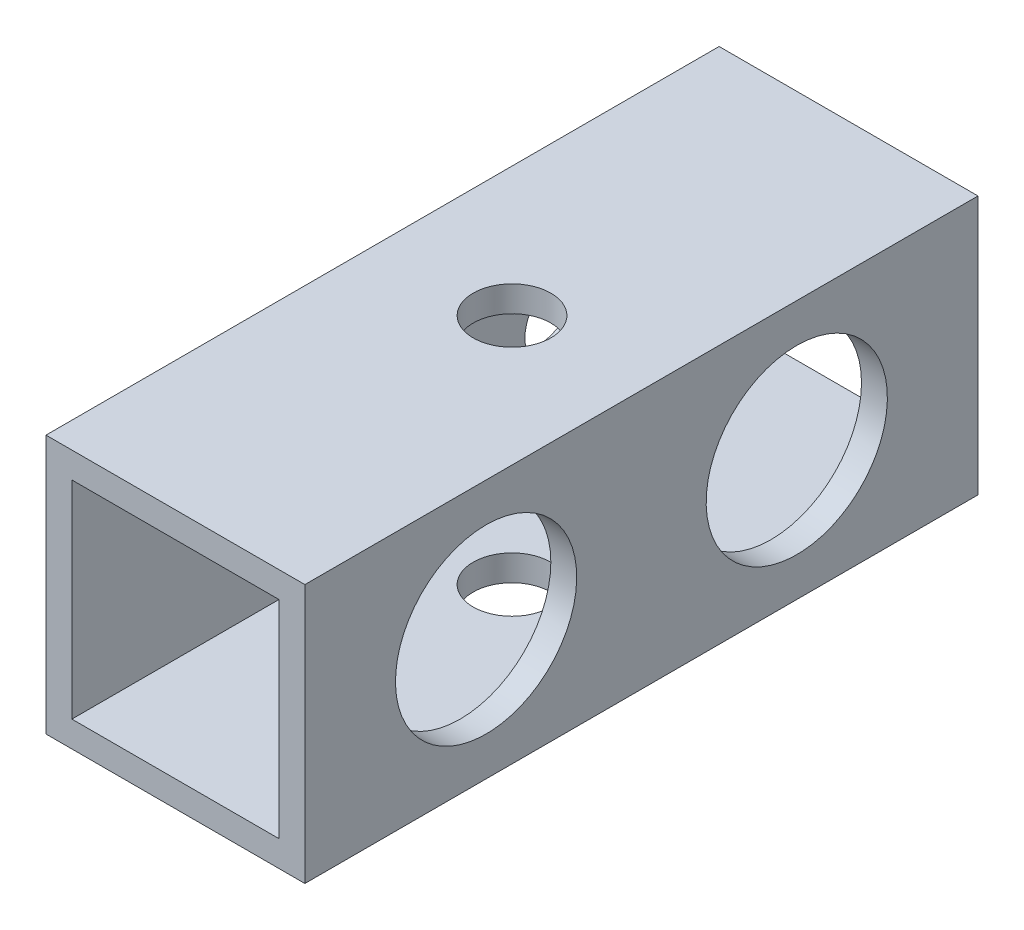
SolidWorks part; units mm, degrees
material "6063-O"
ref_plane "前视基准面" through (0, 0, 0) normal (0, 0, 1) x (1, 0, 0)
ref_plane "上视基准面" through (0, 0, 0) normal (0, 1, 0) x (1, 0, 0)
ref_plane "右视基准面" through (0, 0, 0) normal (1, 0, 0) x (0, 0, -1)
other "Configuration Table"
sketch "草图1" plane through (0, 0, 0) normal (0, 0, 1) x (1, 0, 0)
  line L1 (5, 5) -> (-5, 5)
  line L2 (5, 5) -> (5, -5)
  line L3 (5, -5) -> (-5, -5)
  line L4 (-5, 5) -> (-5, -5)
  line L5 (5, 5) -> (-5, -5) construction
  line L6 (5, -5) -> (-5, 5) construction
  point P4 (0, 0)
  dimension "D1" = 10
  dimension "D2" = 10
extrude "拉伸-薄壁1" add sketch "草图1" along normal blind 26 thin thin type one direction reverse wall 1
sketch "草图2" plane through (-5, 0, 0) normal (-1, 0, 0) x (0, 0, 1)
  line L0 (0, 0) -> (26, 0) construction
  line L1 (0, 5) -> (0, -5) construction
  line L2 (26, 5) -> (26, -5) construction
  line L3 (13, -5) -> (13, 0) construction
  line L4 (26, -5) -> (0, -5) construction
  circle A0 centre (7, 0) radius 1.5
  circle A1 centre (19, 0) radius 1.5
  dimension "D1" = 7
  dimension "D2" = 3
  dimension "D3" = 12
extrude "切除-拉伸1" cut sketch "草图2" against normal blind 10
sketch "草图3" plane through (0, -5, 0) normal (0, -1, 0) x (1, 0, 0)
  line L0 (0, 26) -> (0, 0) construction
  line L1 (-5, 26) -> (5, 26) construction
  line L3 (-5, 0) -> (5, 0) construction
  circle A0 centre (0, 13) radius 1.5
  dimension "D1" = 3
  dimension "D2" = 13
extrude "切除-拉伸2" cut sketch "草图3" against normal blind 10
sketch "草图4" plane through (5, 0, 0) normal (1, 0, 0) x (0, 0, -1)
  circle A0 centre (-19, 0) radius 3.5
  circle A1 centre (-7, 0) radius 3.5
  dimension "D1" = 7
extrude "切除-拉伸3" cut sketch "草图4" against normal blind 5
